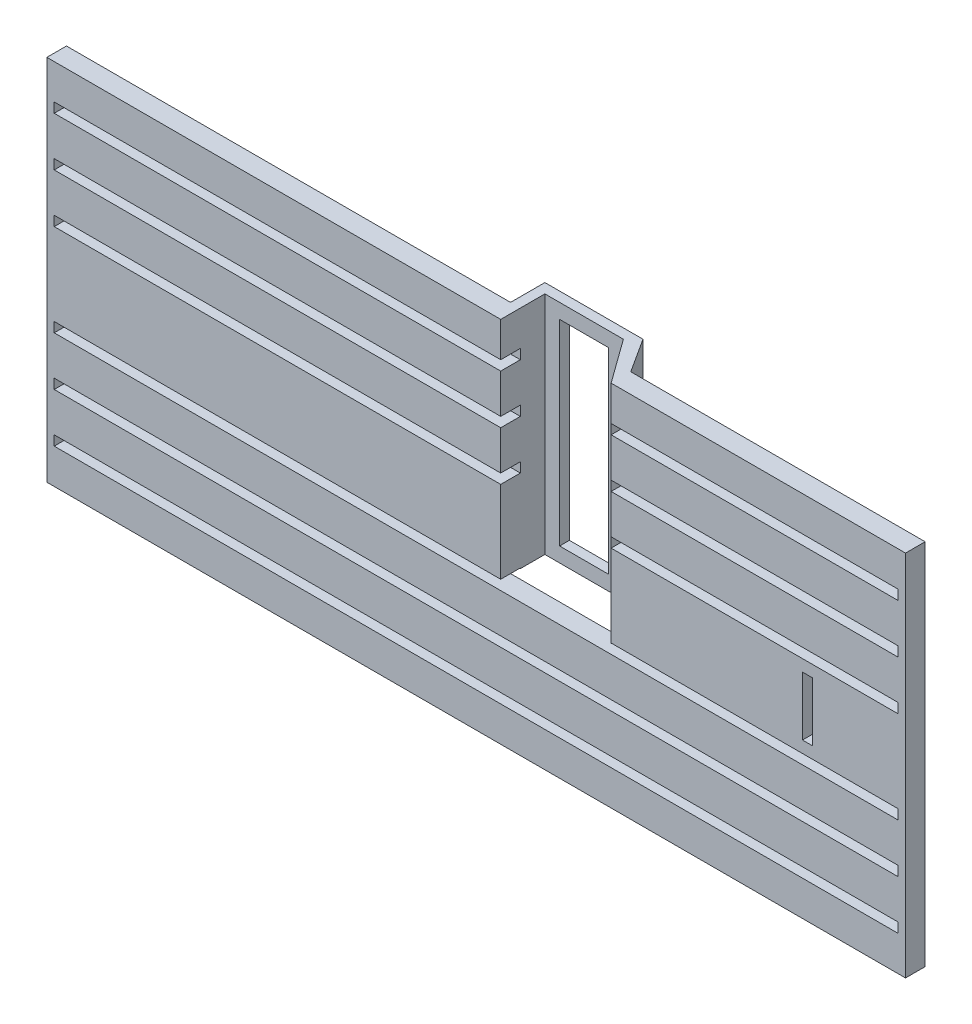
SolidWorks part; units mm, degrees
ref_plane "Front Plane" through (0, 0, 0) normal (0, 0, 1) x (1, 0, 0)
ref_plane "Top Plane" through (0, 0, 0) normal (0, 1, 0) x (1, 0, 0)
ref_plane "Right Plane" through (0, 0, 0) normal (1, 0, 0) x (0, 0, -1)
sketch "Sketch1" plane through (0, 0, 0) normal (0, 0, 1) x (1, 0, 0)
  line L1 (111.125, -47.625) -> (-111.125, -47.625)
  line L2 (111.125, -47.625) -> (111.125, 47.625)
  line L3 (111.125, 47.625) -> (-111.125, 47.625)
  line L4 (-111.125, -47.625) -> (-111.125, 47.625)
  line L5 (111.125, -47.625) -> (-111.125, 47.625) construction
  line L6 (111.125, 47.625) -> (-111.125, -47.625) construction
  point P0 (0, 0)
  dimension "D1" = 95.25
  dimension "D2" = 222.25
extrude "Boss-Extrude1" add sketch "Sketch1" along normal blind 5.08
sketch "Sketch2" plane through (0, 0, 0) normal (0, 0, -1) x (-1, 0, 0)
  line L0 (0, 47.625) -> (0, -47.625) construction
  line L1 (-111.125, 47.625) -> (111.125, 47.625) construction
  line L2 (111.125, -47.625) -> (-111.125, -47.625) construction
  line L3 (111.125, 0) -> (-111.125, 0) construction
  line L4 (111.125, 47.625) -> (111.125, -47.625) construction
  line L5 (-111.125, -47.625) -> (-111.125, 47.625) construction
  line L6 (0, 0) -> (0, 47.625) construction
  line L7 (0, 0) -> (0, -47.625) construction
  line L8 (0, -23.8125) -> (0, -47.625) construction
  line L9 (0, -23.8125) -> (0, 0) construction
  line L10 (0, -23.8125) -> (0, -47.625) construction
  line L11 (0, 0) -> (0, 47.625) construction
  line L12 (0, 23.8125) -> (0, 47.625) construction
  line L13 (0, 23.8125) -> (0, 0) construction
  line L14 (0, 0) -> (0, 23.8125) construction
  line L15 (-109.22, 25.8763) -> (109.22, 25.8763)
  line L16 (-109.22, 13.1763) -> (109.22, 13.1763)
  line L17 (-109.22, 13.1763) -> (-109.22, 10.6363)
  line L18 (-109.22, 10.6363) -> (109.22, 10.6363)
  line L19 (109.22, 13.1763) -> (109.22, 10.6363)
  line L20 (-109.22, 13.1763) -> (109.22, 10.6363) construction
  line L21 (-109.22, 10.6363) -> (109.22, 13.1763) construction
  line L22 (-109.22, 23.3363) -> (109.22, 23.3363)
  line L23 (-109.22, 25.8763) -> (-109.22, 23.3363)
  line L24 (109.22, 25.8763) -> (109.22, 23.3363)
  line L25 (-109.22, 38.5763) -> (109.22, 38.5763)
  line L26 (-109.22, 36.0363) -> (109.22, 36.0363)
  line L27 (-109.22, 38.5763) -> (-109.22, 36.0363)
  line L28 (109.22, 38.5763) -> (109.22, 36.0363)
  line L29 (109.22, -13.1763) -> (109.22, -10.6363)
  line L30 (-109.22, -10.6362) -> (109.22, -10.6363)
  line L31 (-109.22, -13.1762) -> (109.22, -13.1763)
  line L32 (-109.22, -13.1762) -> (-109.22, -10.6362)
  line L33 (-109.22, -25.8762) -> (-109.22, -23.3362)
  line L34 (-109.22, -23.3362) -> (109.22, -23.3363)
  line L35 (-109.22, -25.8762) -> (109.22, -25.8763)
  line L36 (109.22, -25.8763) -> (109.22, -23.3363)
  line L37 (109.22, -38.5763) -> (109.22, -36.0363)
  line L38 (-109.22, -38.5762) -> (-109.22, -36.0362)
  line L39 (-109.22, -38.5762) -> (109.22, -38.5763)
  line L40 (-109.22, -36.0362) -> (109.22, -36.0363)
  point P16 (0, 11.9063)
  dimension "D1" = 2.54
  dimension "D2" = 218.44
  dimension "D3" = 3
extrude "Cut-Extrude1" cut sketch "Sketch2" against normal blind 5.08
sketch "Sketch5" plane through (0, 0, 0) normal (0, 0, -1) x (-1, 0, 0)
  line L0 (-111.125, 0) -> (-85.725, 0) construction
  line L1 (-111.125, -47.625) -> (-111.125, 47.625) construction
  line L3 (-86.995, 7.62) -> (-84.455, 7.62)
  line L4 (-86.995, 7.62) -> (-86.995, -7.62)
  line L5 (-86.995, -7.62) -> (-84.455, -7.62)
  line L6 (-84.455, 7.62) -> (-84.455, -7.62)
  line L7 (-86.995, 7.62) -> (-84.455, -7.62) construction
  line L8 (-86.995, -7.62) -> (-84.455, 7.62) construction
  point P9 (-85.725, -7.62)
  dimension "D1" = 25.4
  dimension "D2" = 15.24
  dimension "D3" = 2.54
extrude "Cut-Extrude4" cut sketch "Sketch5" against normal blind 5.08
sketch "Sketch6" plane through (0, 47.625, 0) normal (0, 1, 0) x (1, 0, 0)
  line L0 (111.125, 0) -> (34.925, 0) construction
  line L1 (111.125, 0) -> (-111.125, 0) construction
  dimension "D1" = 76.2
sketch "Sketch7" plane through (0, 0, 0) normal (0, 0, -1) x (-1, 0, 0)
  line L0 (-111.125, 47.625) -> (-34.925, 47.625) construction
  line L1 (-34.925, 47.625) -> (-6.35, 47.625)
  line L2 (-34.925, 47.625) -> (-34.925, 25.8763)
  line L3 (-34.925, 25.8763) -> (-6.35, 25.8763)
  line L4 (-6.35, 47.625) -> (-6.35, 25.8763)
  line L5 (-111.125, 47.625) -> (111.125, 47.625) construction
  line L6 (109.22, 25.8763) -> (-109.22, 25.8763) construction
  dimension "D1" = 28.575
extrude "Cut-Extrude5" cut sketch "Sketch7" against normal blind 5.08
sketch "Sketch8" plane through (0, 0, 0) normal (0, 0, -1) x (-1, 0, 0)
  line L0 (-34.925, 47.625) -> (-34.925, -62.7102) construction
  line L1 (-109.22, 10.6363) -> (109.22, 10.6363) construction
  line L2 (-34.925, 10.6363) -> (-6.35, 10.6363)
  line L3 (-34.925, 10.6363) -> (-34.925, -10.6362)
  line L4 (-34.925, -10.6362) -> (-6.35, -10.6363)
  line L5 (-6.35, 10.6363) -> (-6.35, -10.6363)
  line L6 (109.22, -10.6363) -> (-109.22, -10.6362) construction
  dimension "D1" = 28.575
extrude "Cut-Extrude6" cut sketch "Sketch8" against normal blind 5.08
sketch "Sketch10" plane through (0, 47.625, 0) normal (0, 1, 0) x (1, 0, 0)
  line L0 (6.35, 0) -> (6.35, 6.35)
  line L1 (6.35, 0) -> (3.81, 0)
  line L2 (6.35, 0) -> (-111.125, 0) construction
  line L6 (3.81, 0) -> (3.81, 8.89)
  line L10 (6.35, 6.35) -> (26.67, 6.35)
  line L11 (3.81, 8.89) -> (29.21, 8.89)
  line L12 (26.67, 6.35) -> (34.925, -5.08)
  line L13 (29.21, 8.89) -> (34.925, 0)
  line L14 (34.925, 0) -> (34.925, -5.08)
  dimension "D1" = 6.35
  dimension "D2" = 2.54
  dimension "D3" = 8.89
  dimension "D4" = 20.32
  dimension "D5" = 25.4
sketch "Sketch11" plane through (0, 0, 0) normal (0, 0, -1) x (-1, 0, 0)
  line L0 (-6.35, 43.2441) -> (-6.35, 8.5084) construction
  line L3 (-6.35, -10.6363) -> (-6.35, 10.6363) construction
  line L4 (109.22, 13.1763) -> (-109.22, 13.1763) construction
  line L5 (-6.35, 13.1763) -> (-34.925, 13.1763)
  line L6 (-6.35, 13.1763) -> (-6.35, 23.3363)
  line L7 (-6.35, 23.3363) -> (-34.925, 23.3363)
  line L8 (-34.925, 13.1763) -> (-34.925, 23.3363)
  line L9 (-109.22, 23.3363) -> (109.22, 23.3363) construction
  point P4 (-6.35, 25.8763)
  dimension "D1" = 28.575
extrude "Cut-Extrude8" cut sketch "Sketch11" against normal blind 5.08
extrude "Boss-Extrude2" add sketch "Sketch10" against normal blind 58.42
sketch "Sketch12" plane through (0, 0, -6.35) normal (0, 0, 1) x (1, 0, 0)
  line L0 (16.51, 47.625) -> (16.51, -10.795) construction
  line L1 (6.35, 47.625) -> (26.67, 47.625) construction
  line L2 (6.35, -10.795) -> (26.67, -10.795) construction
  line L4 (22.86, 43.815) -> (10.16, 43.815)
  line L5 (22.86, 43.815) -> (22.86, -6.985)
  line L6 (22.86, -6.985) -> (10.16, -6.985)
  line L7 (10.16, 43.815) -> (10.16, -6.985)
  line L8 (22.86, 43.815) -> (10.16, -6.985) construction
  line L9 (22.86, -6.985) -> (10.16, 43.815) construction
  point P6 (16.51, 18.415)
  dimension "D1" = 12.7
  dimension "D2" = 50.8
extrude "Cut-Extrude9" cut sketch "Sketch12" against normal blind 2.54
